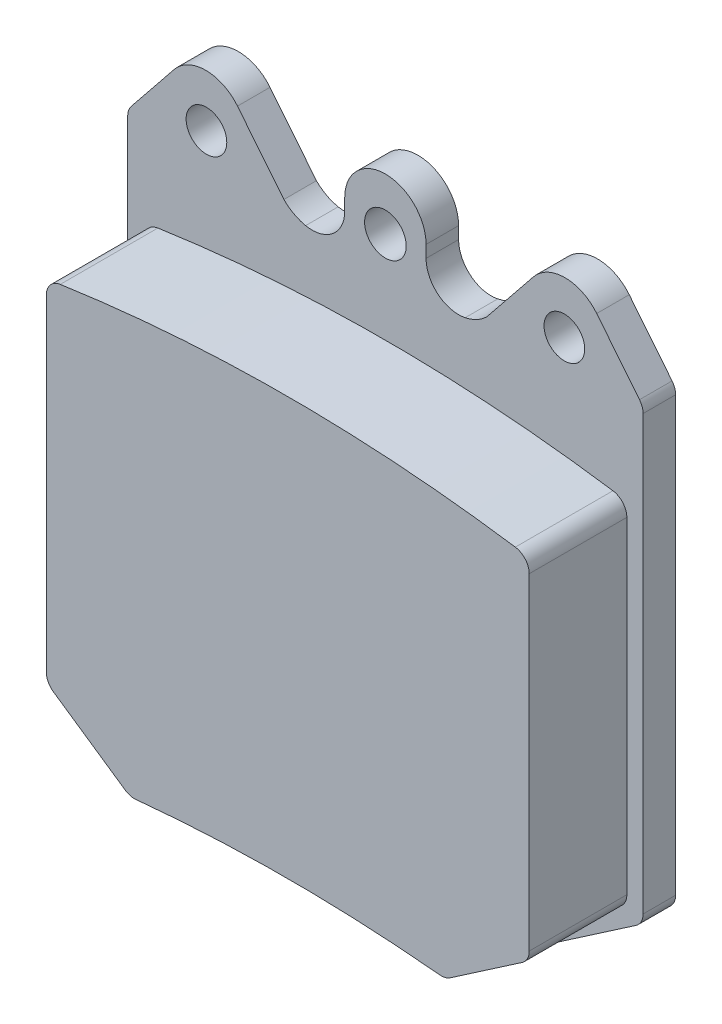
SolidWorks part; units mm, degrees
material "C (Graphite)"
ref_plane "Front Plane" through (0, 0, 0) normal (0, 0, 1) x (1, 0, 0)
ref_plane "Top Plane" through (0, 0, 0) normal (0, 1, 0) x (1, 0, 0)
ref_plane "Right Plane" through (0, 0, 0) normal (1, 0, 0) x (0, 0, -1)
sketch "Sketch1" plane through (0, 0, 0) normal (0, 0, 1) x (1, 0, 0)
  line L1 (0, 0) -> (50.292, 0)
  line L2 (0, 0) -> (0, -57.15)
  line L3 (0, -57.15) -> (50.292, -57.15)
  line L4 (50.292, 0) -> (50.292, -57.15)
  dimension "D1" = 57.15
  dimension "D2" = 50.292
extrude "Boss-Extrude1" add sketch "Sketch1" along normal blind 3.175
sketch "Sketch3" plane through (0, 0, 3.175) normal (0, 0, 1) x (1, 0, 0)
  line L0 (0, 0) -> (0, -57.15) construction
  line L1 (50.292, 0) -> (0, 0) construction
  line L2 (25.146, 0) -> (25.146, -13.8357) construction
  line L3 (50.292, -57.15) -> (50.292, 0) construction
  line L4 (0, -57.15) -> (9.271, -57.15)
  line L5 (0, -57.15) -> (50.292, -57.15) construction
  line L6 (0, -57.15) -> (0, -50.8)
  line L7 (0, -50.8) -> (9.271, -57.15)
  line L8 (50.292, -50.8) -> (41.021, -57.15)
  line L9 (50.292, -57.15) -> (50.292, -50.8)
  line L10 (50.292, -57.15) -> (41.021, -57.15)
  circle A0 centre (25.146, -5.08) radius 2.032
  circle A1 centre (42.6085, -5.08) radius 1.9844
  circle A2 centre (7.6835, -5.08) radius 1.9844
  dimension "D1" = 4.064
  dimension "D2" = 25.146
  dimension "D4" = 3.9688
  dimension "D5" = 3.9688
  dimension "D3" = 5.08
  dimension "D6" = 5.08
  dimension "D7" = 5.08
  dimension "D8" = 34.925
  dimension "D9" = 17.4625
  dimension "D10" = 9.271
  dimension "D11" = 9.271
  dimension "D12" = 6.35
  dimension "D13" = 6.35
extrude "Cut-Extrude1" cut sketch "Sketch3" against normal through all
sketch "Sketch4" plane through (0, 0, 3.175) normal (0, 0, 1) x (1, 0, 0)
  line L0 (50.292, 0) -> (0, 0) construction
  line L1 (21.1772, -3.9688) -> (21.1772, -5.1456)
  line L2 (29.1147, -3.9688) -> (29.1147, -5.1456)
  line L3 (0, 0) -> (50.292, 0)
  line L4 (0, 0) -> (0, -50.8) construction
  line L5 (50.292, -50.8) -> (50.292, 0) construction
  line L6 (45.7649, -1.4818) -> (50.292, -7.112)
  line L7 (4.5271, -1.4818) -> (0, -7.112)
  line L8 (50.292, -7.112) -> (50.292, 0)
  line L10 (0, -7.112) -> (0, 0)
  line L12 (10.7129, -1.4818) -> (15.24, -7.112)
  line L13 (39.5791, -1.4818) -> (35.052, -7.112)
  arc A0 (29.1147, -3.9688) -> (21.1772, -3.9688) centre (25.146, -3.9688) ccw
  arc A1 (29.1147, -5.1456) -> (32.9301, -8.2554) centre (32.2897, -5.1456) ccw
  arc A2 (10.7129, -1.4818) -> (4.5271, -1.4818) centre (7.62, -3.9688) ccw
  arc A3 (45.7649, -1.4818) -> (39.5791, -1.4818) centre (42.672, -3.9688) ccw
  arc A4 (15.24, -7.112) -> (17.3619, -8.2554) centre (18.2086, -4.1434) ccw
  arc A5 (35.052, -7.112) -> (32.9301, -8.2554) centre (32.0834, -4.1434) cw
  arc A6 (17.3619, -8.2554) -> (21.1772, -5.1456) centre (18.0022, -5.1456) ccw
  dimension "D1" = 7.9375
  dimension "D2" = 7.9375
  dimension "D3" = 7.9375
  dimension "D6" = 3.175
  dimension "D4" = 7.62
  dimension "D5" = 7.62
extrude "Cut-Extrude2" cut sketch "Sketch4" against normal through all
fillet "Fillet1" radius 1.5875 6 edges at (9.271, -57.15, 1.5875) (0, -50.8, 1.5875) (41.021, -57.15, 1.5875) (50.292, -50.8, 1.5875) (50.292, -7.112, 1.5875) (0, -7.112, 1.5875)
sketch "Sketch6" plane through (0, 0, 3.175) normal (0, 0, 1) x (1, 0, 0)
  line L0 (0, -7.6711) -> (0, -49.9632) construction
  line L3 (8.8655, -56.8722) -> (0.6904, -51.2729) construction
  line L4 (49.6016, -51.2729) -> (41.4265, -56.8722) construction
  line L5 (50.292, -49.9632) -> (50.292, -7.6711) construction
  line L6 (1.5875, -17.2396) -> (1.5875, -49.1263)
  line L7 (2.2779, -50.436) -> (9.2846, -55.2352)
  line L9 (41.0074, -55.2352) -> (48.0141, -50.436)
  line L10 (48.7045, -49.1263) -> (48.7045, -17.2396)
  arc A1 (2.9437, -15.669) -> (47.3483, -15.669) centre (25.146, -166.4431) cw
  arc A2 (10.336, -55.5054) -> (39.956, -55.5054) centre (25.146, -207.1841) cw
  arc A3 (2.9437, -15.669) -> (1.5875, -17.2396) centre (3.175, -17.2396) ccw
  arc A4 (2.2779, -50.436) -> (1.5875, -49.1263) centre (3.175, -49.1263) cw
  arc A5 (9.2846, -55.2352) -> (10.336, -55.5054) centre (10.1817, -53.9254) ccw
  arc A6 (41.0074, -55.2352) -> (39.956, -55.5054) centre (40.1103, -53.9254) cw
  arc A7 (48.0141, -50.436) -> (48.7045, -49.1263) centre (47.117, -49.1263) ccw
  arc A8 (48.7045, -17.2396) -> (47.3483, -15.669) centre (47.117, -17.2396) ccw
  dimension "D7" = 152.4
  dimension "D8" = 152.4
  dimension "D2" = 1.5875
  dimension "D1" = 1.5875
  dimension "D3" = 1.5875
  dimension "D4" = 1.5875
  dimension "D5" = 1.5875
extrude "Boss-Extrude2" add sketch "Sketch6" along normal blind 9.525
